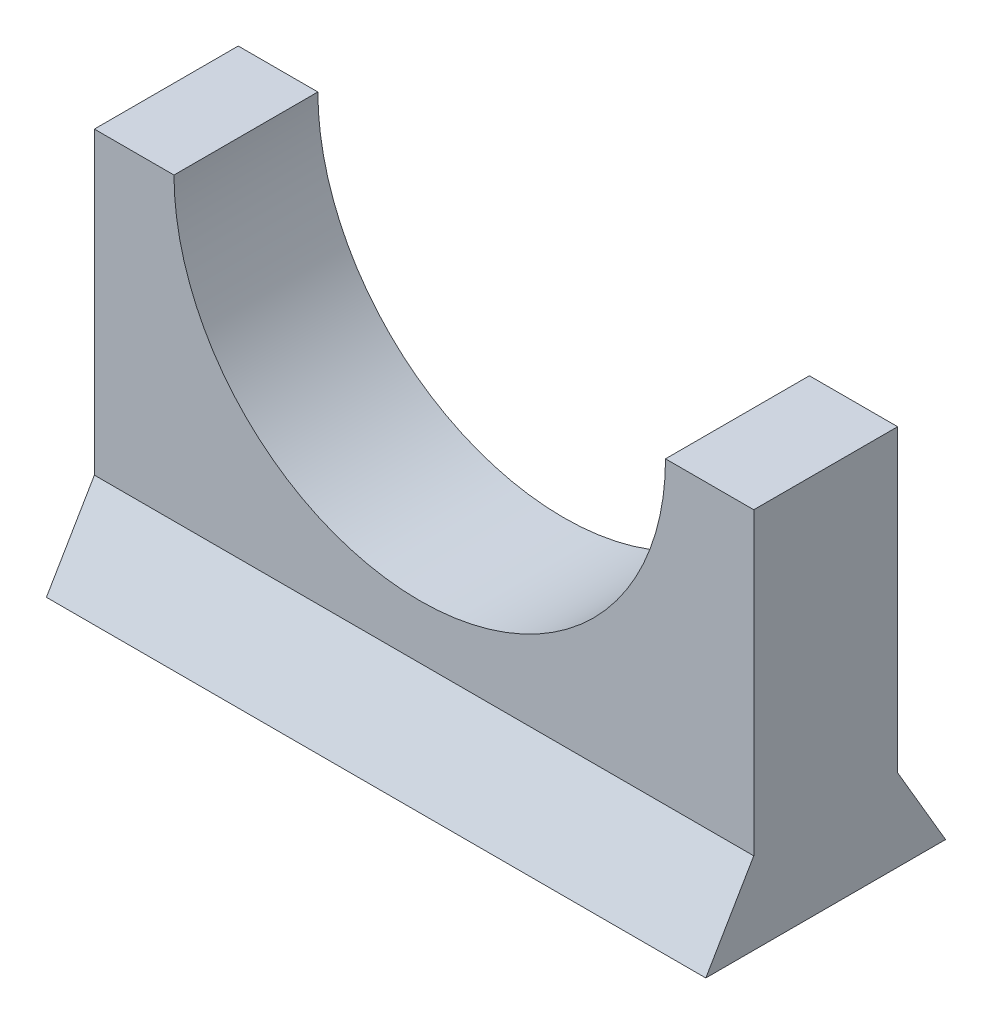
SolidWorks part; units mm, degrees
ref_plane "Front Plane" through (0, 0, 0) normal (0, 0, 1) x (1, 0, 0)
ref_plane "Top Plane" through (0, 0, 0) normal (0, 1, 0) x (1, 0, 0)
ref_plane "Right Plane" through (0, 0, 0) normal (1, 0, 0) x (0, 0, -1)
sketch "Sketch1" plane through (0, 0, 0) normal (0, 0, 1) x (1, 0, 0)
  line L1 (0, 0) -> (139.7, 0)
  line L2 (0, 0) -> (0, 76.2)
  line L3 (0, 76.2) -> (139.7, 76.2)
  line L4 (139.7, 0) -> (139.7, 76.2)
  dimension "D1" = 139.7
  dimension "D2" = 76.2
extrude "Boss-Extrude1" add sketch "Sketch1" along normal blind 50.8
sketch "Sketch2" plane through (139.7, 0, 0) normal (1, 0, 0) x (0, 0, -1)
  line L0 (-50.8, 0) -> (0, 0)
  line L1 (-25.4, 0) -> (-25.4, 42.8589)
  line L2 (-25.4, 17.3352) -> (-10.16, 17.3352)
  line L3 (-25.4, 17.3352) -> (-40.64, 17.3352)
  line L4 (-10.16, 17.3352) -> (0, 0)
  line L5 (-40.64, 17.3352) -> (-50.8, 0)
  line L6 (-50.8, 0) -> (-50.8, 76.2)
  line L7 (-50.8, 76.2) -> (0, 76.2)
  line L8 (0, 76.2) -> (0, 0)
  dimension "D1" = 15.24
  dimension "D2" = 15.24
extrude "Cut-Extrude1" cut sketch "Sketch2" against normal through all
sketch "Sketch3" plane through (0, 17.3352, 0) normal (0, 1, 0) x (1, 0, 0)
  line L0 (0, -25.4) -> (139.7, -25.4)
  line L1 (0, -10.16) -> (0, -40.64) construction
  line L2 (139.7, -10.16) -> (139.7, -40.64) construction
  line L4 (0, -40.64) -> (139.7, -40.64)
  line L5 (0, -40.64) -> (0, -10.16)
  line L6 (0, -10.16) -> (139.7, -10.16)
  line L7 (139.7, -40.64) -> (139.7, -10.16)
  line L8 (0, -40.64) -> (139.7, -10.16) construction
  line L9 (0, -10.16) -> (139.7, -40.64) construction
  point P6 (69.85, -25.4)
  line M1 (139.7, -40.64) -> (139.7, -10.16)
  line M2 (139.7, -10.16) -> (0, -10.16)
  line M3 (0, -10.16) -> (0, -40.64)
  line M4 (0, -40.64) -> (139.7, -40.64)
extrude "Boss-Extrude2" add sketch "Sketch3" along normal blind 63.5 contours L0 M3 M4 M1 | L0 M3 M1 M2
sketch "Sketch7" plane through (0, 0, 40.64) normal (0, 0, 1) x (1, 0, 0)
  line L0 (16.8653, 80.8352) -> (121.0053, 80.8352)
  line L1 (0, 80.8352) -> (139.7, 80.8352) construction
  arc A0 (16.8653, 80.8352) -> (121.0053, 80.8352) centre (68.9353, 80.8352) ccw
  point P5 (68.9353, 80.8352)
  dimension "D1" = 104.14
extrude "Cut-Extrude4" cut sketch "Sketch7" against normal blind 63.5
